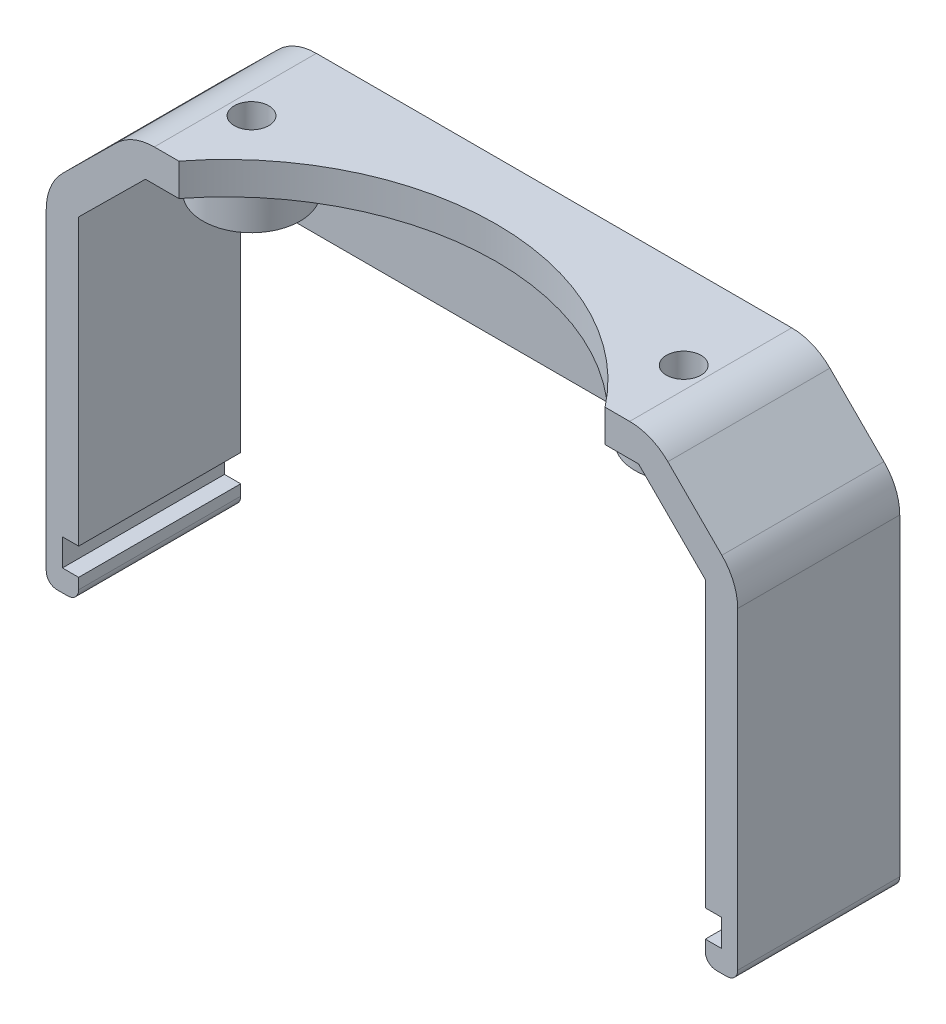
SolidWorks part; units mm, degrees
ref_plane "Alzado" through (0, 0, 0) normal (0, 0, 1) x (1, 0, 0)
ref_plane "Planta" through (0, 0, 0) normal (0, 1, 0) x (1, 0, 0)
ref_plane "Vista lateral" through (0, 0, 0) normal (1, 0, 0) x (0, 0, -1)
sketch "Croquis1" plane through (0, 0, 0) normal (0, 0, 1) x (1, 0, 0)
  line L0 (29, 27) -> (29, 60.3405) construction
  line L1 (51, 35) -> (7, 35) construction
  line L2 (51.8284, 37) -> (6.1783, 37)
  line L4 (0, 30.8923) -> (6.1783, 37)
  line L5 (51.8284, 37) -> (58, 30.8284)
  line L36 (59.5, 2) -> (58, 2)
  line L37 (59.5, 4.5) -> (59.5, 2)
  line L38 (58, 4.5) -> (59.5, 4.5)
  line L39 (58, 30.8284) -> (58, 4.5)
  line L40 (0, 27) -> (58, 27) construction
  line L41 (0, 4.5) -> (0, 30.8923)
  line L42 (-1.5, 4.5) -> (0, 4.5)
  line L43 (-1.5, 2) -> (-1.5, 4.5)
  line L44 (0, 2) -> (-1.5, 2)
  line L45 (0, 1) -> (0, 2)
  line L46 (-2, 0) -> (-1, 0)
  line L47 (-3, 30) -> (-3, 1)
  line L48 (3.4848, 38.5558) -> (-1.4745, 33.6531)
  line L49 (51, 40) -> (7, 40)
  line L50 (59.5355, 33.5355) -> (54.5355, 38.5355)
  line L51 (61, 1) -> (61, 30)
  line L52 (59, 0) -> (60, 0)
  line L53 (58, 2) -> (58, 1)
  arc A16 (-1, 0) -> (0, 1) centre (-1, 1) ccw
  arc A17 (-3, 1) -> (-2, 0) centre (-2, 1) ccw
  arc A18 (-1.4745, 33.6531) -> (-3, 30) centre (2.1368, 30) ccw
  arc A19 (7, 40) -> (3.4848, 38.5558) centre (7, 35) ccw
  arc A20 (54.5355, 38.5355) -> (51, 40) centre (51, 35) ccw
  arc A21 (61, 30) -> (59.5355, 33.5355) centre (56, 30) ccw
  arc A22 (60, 0) -> (61, 1) centre (60, 1) ccw
  arc A23 (58, 1) -> (59, 0) centre (59, 1) ccw
  dimension "D9" = 1
  dimension "D10" = 1
  dimension "D2" = 3
  dimension "D1" = 64
  dimension "D3" = 3
  dimension "D4" = 3
  dimension "D5" = 44
  dimension "D6" = 22
  dimension "D7" = 2.5
  dimension "D8" = 1.5
  dimension "D11" = 40
  dimension "D14" = 3
  dimension "D15" = 3
  dimension "D12" = 2
ref_plane "Plano1" through (0, 40, 0) normal (0, 1, 0) x (1, 0, 0)
sketch "Croquis2" plane through (0, 40, 0) normal (0, 1, 0) x (1, 0, 0)
  line L0 (-9.9879, -8) -> (68.6591, -8) construction
  line L1 (29, 0) -> (29, -23.7021) construction
  line L2 (0, 0) -> (58, 0) construction
  circle A0 centre (9, -8) radius 1.6
  circle A1 centre (49, -8) radius 1.6
  dimension "D2" = 3.2
  dimension "D3" = 3.2
  dimension "D4" = 40
  dimension "D5" = 20
  dimension "D1" = 8
extrude "Saliente-Extruir2" add sketch "Croquis1" along normal blind 15 separate body
sketch "Croquis3" plane through (0, 0, 0) normal (0, 0, 1) x (1, 0, 0)
  line L0 (0, 27) -> (58, 27)
  line L1 (58, 27) -> (58, 30.8284)
  line L2 (58, 30.8284) -> (51.8284, 37)
  line L3 (51.8284, 37) -> (6.1783, 37)
  line L4 (6.1783, 37) -> (0, 30.8923)
  line L5 (0, 30.8923) -> (0, 27)
  line L6 (0, 4.5) -> (0, 30.8923) construction
  line L7 (58, 30.8284) -> (58, 4.5) construction
extrude "Saliente-Extruir3" add sketch "Croquis3" along normal blind 1.5
extrude "Cortar-Extruir1" cut sketch "Croquis2" against normal blind 10
sketch "Croquis4" plane through (0, 37, 0) normal (0, -1, 0) x (1, 0, 0)
  line L0 (10.525, 10.6414) -> (7.475, 10.6414)
  line L1 (7.475, 10.6414) -> (5.95, 8)
  line L2 (5.95, 8) -> (7.475, 5.3586)
  line L3 (52.05, 8) -> (50.525, 10.6414)
  line L4 (50.525, 10.6414) -> (47.475, 10.6414)
  line L5 (47.475, 10.6414) -> (45.95, 8)
  line L6 (45.95, 8) -> (47.475, 5.3586)
  line L7 (47.475, 5.3586) -> (50.525, 5.3586)
  line L8 (50.525, 5.3586) -> (52.05, 8)
  line L9 (7.475, 5.3586) -> (10.525, 5.3586)
  line L10 (10.525, 5.3586) -> (12.05, 8)
  line L11 (12.05, 8) -> (10.525, 10.6414)
  circle A0 centre (49, 8) radius 3.05 construction
  circle A1 centre (49, 8) radius 4.5
  circle A2 centre (9, 8) radius 4.5
  circle A3 centre (9, 8) radius 3.05 construction
  dimension "D1" = 6.1
  dimension "D2" = 9
  dimension "D3" = 2
extrude "Saliente-Extruir4" add sketch "Croquis4" along normal blind 3.2
sketch "Croquis5" plane through (0, 40, 0) normal (0, 1, 0) x (1, 0, 0)
  line L0 (29, -30.3607) -> (9, -8) construction
  line L1 (29, -30.3607) -> (49, -8) construction
  line L2 (9.2757, -15) -> (48.7243, -15)
  line L3 (51, -15) -> (7, -15) construction
  arc A0 (48.7243, -15) -> (9.2757, -15) centre (29, -30.3607) ccw
  dimension "D1" = 50
  dimension "D2" = 30
extrude "Cortar-Extruir2" cut sketch "Croquis5" against normal up to next
